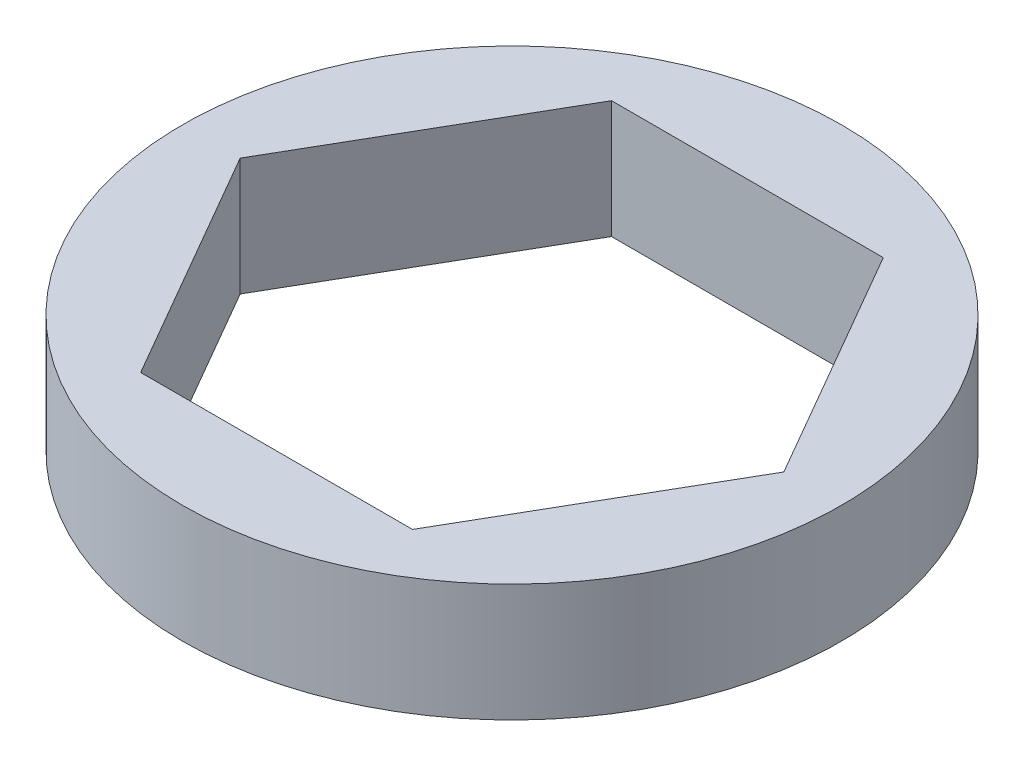
SolidWorks part; units mm, degrees
ref_plane "Front Plane" through (0, 0, 0) normal (0, 0, 1) x (1, 0, 0)
ref_plane "Top Plane" through (0, 0, 0) normal (0, 1, 0) x (1, 0, 0)
ref_plane "Right Plane" through (0, 0, 0) normal (1, 0, 0) x (0, 0, -1)
sketch "Sketch1" plane through (0, 0, 0) normal (0, 1, 0) x (1, 0, 0)
  line L1 (7.3323, 0) -> (3.6662, 6.35)
  line L2 (3.6662, 6.35) -> (-3.6662, 6.35)
  line L3 (-3.6662, 6.35) -> (-7.3323, 0)
  line L4 (-7.3323, 0) -> (-3.6662, -6.35)
  line L5 (-3.6662, -6.35) -> (3.6662, -6.35)
  line L6 (3.6662, -6.35) -> (7.3323, 0)
  circle A0 centre (0, 0) radius 6.35 construction
  circle A1 centre (0, 0) radius 8.89
  dimension "D1" = 12.7
  dimension "D3" = 17.78
  dimension "D2" = 6.35
extrude "Boss-Extrude1" add sketch "Sketch1" along normal blind 3.175
